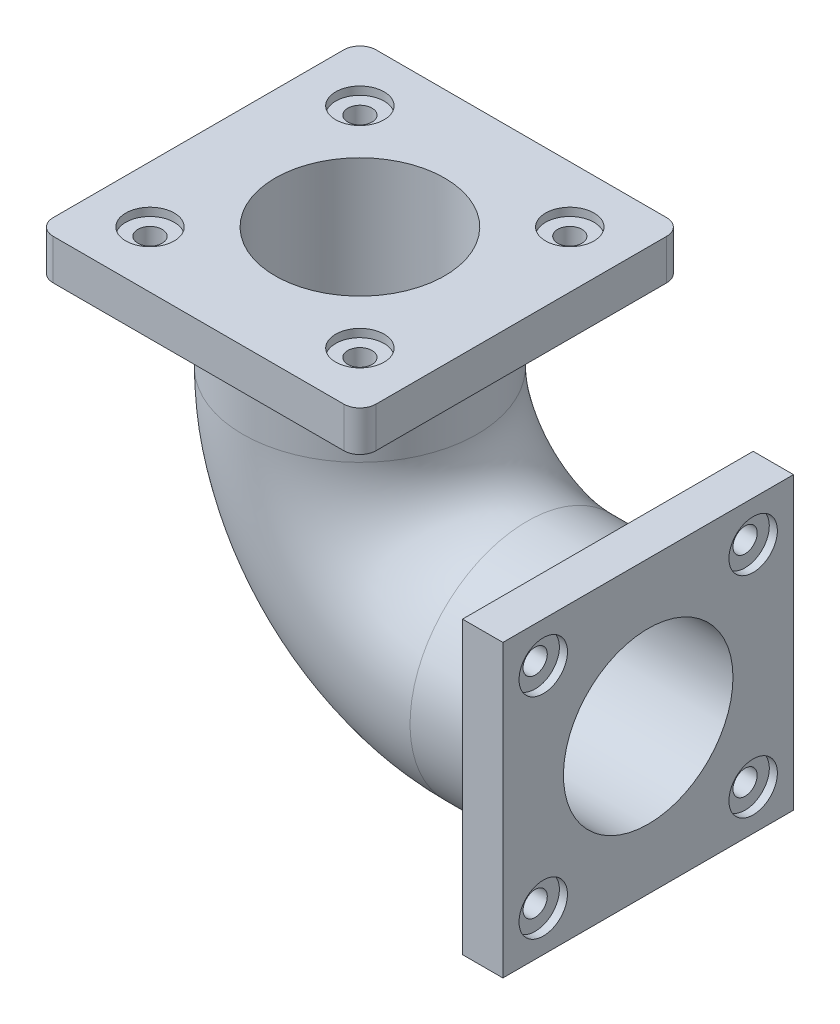
SolidWorks part; units mm, degrees
ref_plane "Front Plane" through (0, 0, 0) normal (0, 0, 1) x (1, 0, 0)
ref_plane "Top Plane" through (0, 0, 0) normal (0, 1, 0) x (1, 0, 0)
ref_plane "Right Plane" through (0, 0, 0) normal (1, 0, 0) x (0, 0, -1)
sketch "Sketch1" plane through (0, 0, 0) normal (0, 0, 1) x (1, 0, 0)
  line L0 (0, 0) -> (-150, 0)
  line L1 (-357.1096, 207.1096) -> (-357.1096, 357.1096)
  arc A0 (-150, 0) -> (-357.1096, 207.1096) centre (-150, 207.1096) cw
  point P5 (0, 0)
  point P7 (0, 0)
  dimension "D2" = 207.1096
  dimension "D1" = 150
sketch "Sketch2" plane through (0, 0, 0) normal (1, 0, 0) x (0, 0, -1)
  circle A0 centre (0, 0) radius 145
  dimension "D1" = 290
sweep "Sweep-Thin2" add profiles "Sketch2" path "Sketch1" parameters "D1"=40
sketch "Sketch5" plane through (0, 0, 0) normal (1, 0, 0) x (0, 0, -1)
  line L1 (-180, 180) -> (180, 180)
  line L2 (-180, 180) -> (-180, -180)
  line L3 (-180, -180) -> (180, -180)
  line L4 (180, 180) -> (180, -180)
  line L5 (-180, 180) -> (180, -180) construction
  line L6 (-180, -180) -> (180, 180) construction
  point P0 (0, 0)
  circle M6 centre (0, 0) radius 145
  dimension "D1" = 360
  dimension "D2" = 360
extrude "Boss-Extrude2" add sketch "Sketch5" against normal blind 50 contours L4 L1 L2 L3 M6
sketch "Sketch6" plane through (0, 357.1096, 0) normal (0, 1, 0) x (1, 0, 0)
  line L0 (-357.1096, 0) -> (-150, 0) construction
  line L1 (-537.1096, 200) -> (-177.1096, 200)
  line L2 (-557.1096, 180) -> (-557.1096, -180)
  line L3 (-537.1096, -200) -> (-177.1096, -200)
  line L4 (-157.1096, 180) -> (-157.1096, -180)
  line L5 (-557.1096, 200) -> (-157.1096, -200) construction
  line L6 (-557.1096, -200) -> (-157.1096, 200) construction
  arc A0 (-557.1096, -180) -> (-537.1096, -200) centre (-537.1096, -180) ccw
  arc A1 (-177.1096, -200) -> (-157.1096, -180) centre (-177.1096, -180) ccw
  arc A2 (-177.1096, 200) -> (-157.1096, 180) centre (-177.1096, 180) cw
  arc A3 (-537.1096, 200) -> (-557.1096, 180) centre (-537.1096, 180) ccw
  point P0 (-357.1096, 0)
  circle M10 centre (-357.1096, 0) radius 145
  dimension "D1" = 20
  dimension "D2" = 360
  dimension "D3" = 360
extrude "Boss-Extrude4" add sketch "Sketch6" against normal blind 50 contours L1 A3 L2 A0 L3 A1 L4 A2 M10
sketch "Sketch12" plane through (0, 357.1096, 0) normal (0, 1, 0) x (1, 0, 0)
  line L6 (-487.1096, 130) -> (-227.1096, 130) construction
  line L7 (-487.1096, 130) -> (-487.1096, -130) construction
  line L8 (-487.1096, -130) -> (-227.1096, -130) construction
  line L9 (-227.1096, 130) -> (-227.1096, -130) construction
  line L10 (-487.1096, 130) -> (-227.1096, -130) construction
  line L11 (-487.1096, -130) -> (-227.1096, 130) construction
  circle A0 centre (-487.1096, 130) radius 30
  point P0 (-357.1096, 0)
  dimension "D3" = 60
  dimension "D1" = 260
  dimension "D2" = 260
extrude "Cut-Extrude2" cut sketch "Sketch12" against normal blind 10 contours A0
sketch "Sketch13" plane through (0, 347.1096, 0) normal (0, 1, 0) x (1, 0, 0)
  circle A0 centre (-487.1096, 130) radius 15
  dimension "D1" = 30
extrude "Cut-Extrude4" cut sketch "Sketch13" against normal up to next (40 mm away)
pattern_circular "CirPattern3" count 4 over 360 about axis through (-357.1096, 0, 0) along (0, 1, 0) of "Cut-Extrude4", "Cut-Extrude2"
sketch "Sketch14" plane through (0, 0, 0) normal (1, 0, 0) x (0, 0, -1)
  line L1 (-130, 130) -> (130, 130) construction
  line L2 (-130, 130) -> (-130, -130) construction
  line L3 (-130, -130) -> (130, -130) construction
  line L4 (130, 130) -> (130, -130) construction
  line L5 (-130, 130) -> (130, -130) construction
  line L6 (-130, -130) -> (130, 130) construction
  circle A0 centre (-130, 130) radius 30
  point P0 (0, 0)
  dimension "D3" = 60
  dimension "D1" = 260
  dimension "D2" = 260
extrude "Cut-Extrude5" cut sketch "Sketch14" against normal blind 10
sketch "Sketch15" plane through (0, 0, 0) normal (1, 0, 0) x (0, 0, -1)
  circle A0 centre (-130, 130) radius 15
  dimension "D1" = 30
extrude "Cut-Extrude6" cut sketch "Sketch15" against normal up to next
pattern_circular "CirPattern4" count 4 over 360 about axis through (0, 0, 0) along (1, 0, 0) of "Cut-Extrude6", "Cut-Extrude5"
